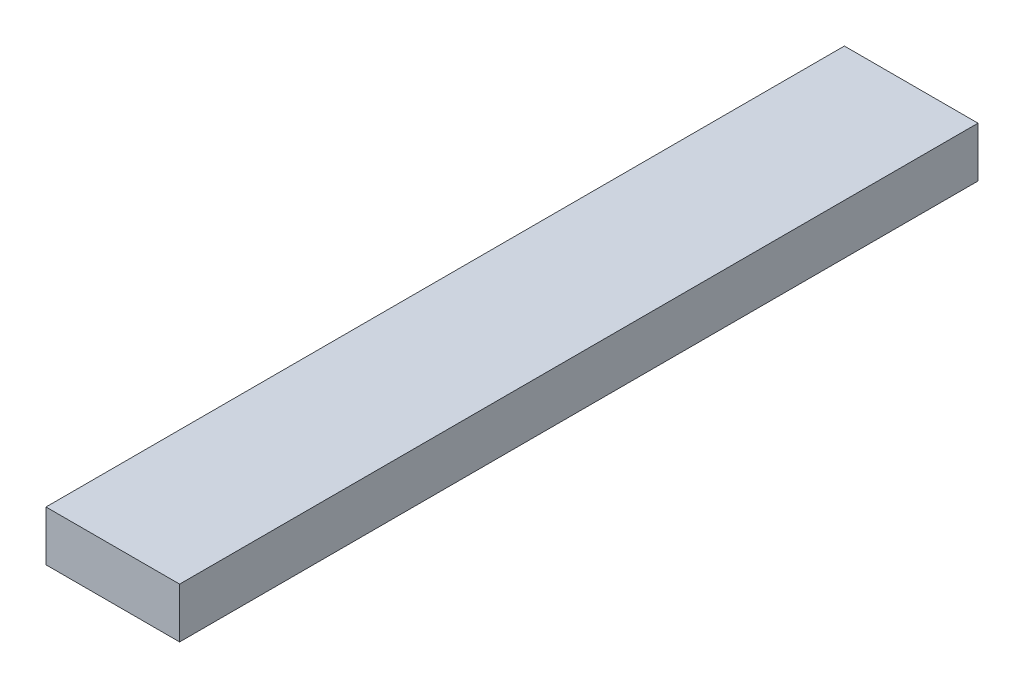
SolidWorks part; units mm, degrees
material "Простая углеродистая сталь"
ref_plane "Спереди" through (0, 0, 0) normal (0, 0, 1) x (1, 0, 0)
ref_plane "Сверху" through (0, 0, 0) normal (0, 1, 0) x (1, 0, 0)
ref_plane "Справа" through (0, 0, 0) normal (1, 0, 0) x (0, 0, -1)
sketch "Эскиз1" plane through (0, 0, 0) normal (0, 1, 0) x (1, 0, 0)
  line L1 (0, 0) -> (80, 0)
  line L2 (0, 0) -> (0, 478)
  line L3 (0, 478) -> (80, 478)
  line L4 (80, 0) -> (80, 478)
extrude "Бобышка-Вытянуть1" add sketch "Эскиз1" along normal blind 30
